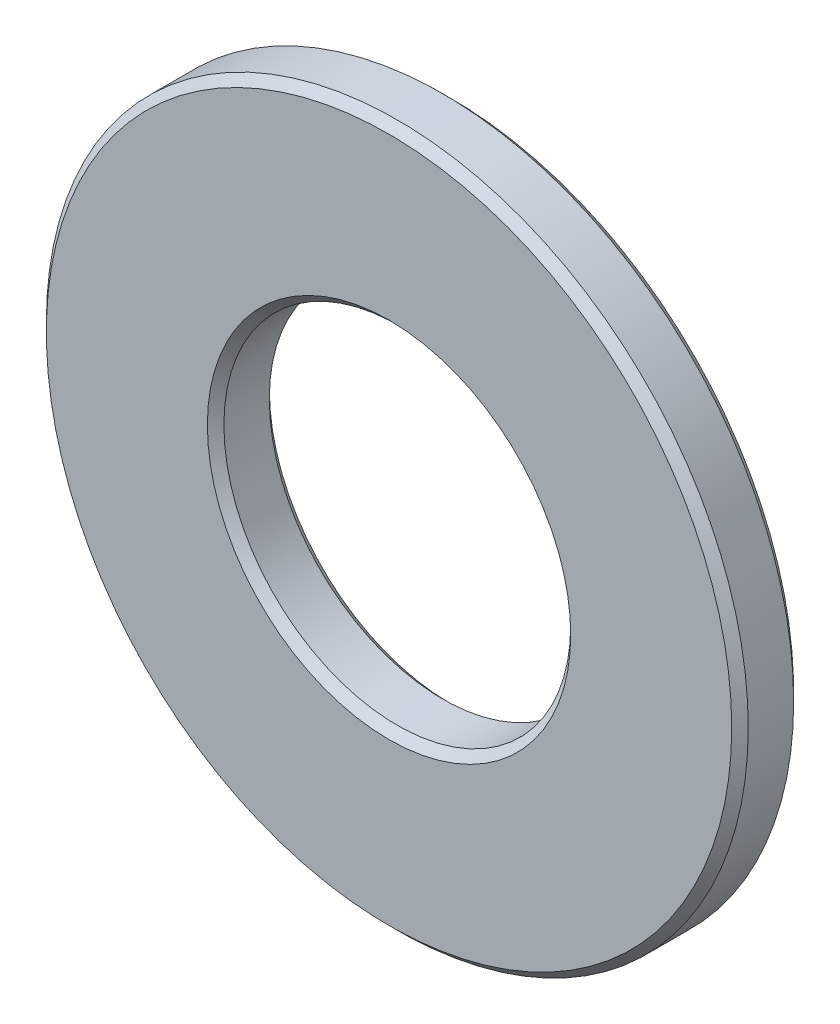
SolidWorks part; units mm, degrees
ref_plane "Front Plane" through (0, 0, 0) normal (0, 0, 1) x (1, 0, 0)
ref_plane "Top Plane" through (0, 0, 0) normal (0, 1, 0) x (1, 0, 0)
ref_plane "Right Plane" through (0, 0, 0) normal (1, 0, 0) x (0, 0, -1)
sketch "Sketch1" plane through (0, 0, 0) normal (0, 1, 0) x (1, 0, 0)
  line L0 (0, 0) -> (0, 22.0371) construction
  line L1 (0, 0) -> (4.2, 0) construction
  line L2 (4.2, 0.75) -> (8.5, 0.75)
  line L3 (4.2, 0.75) -> (4.2, -0.75)
  line L4 (4.2, -0.75) -> (8.5, -0.75)
  line L5 (8.5, 0.75) -> (8.5, -0.75)
  dimension "D1" = 1.5
  dimension "D2" = 8.4
  dimension "D3" = 17
revolve "Revolve1" add sketch "Sketch1" angle 360 about L0
chamfer "Chamfer1" distance 0.2 angle 45 4 edges at (8.5, 0, 0.75) (8.5, 0, -0.75) (4.2, 0, -0.75) (4.2, 0, 0.75)
